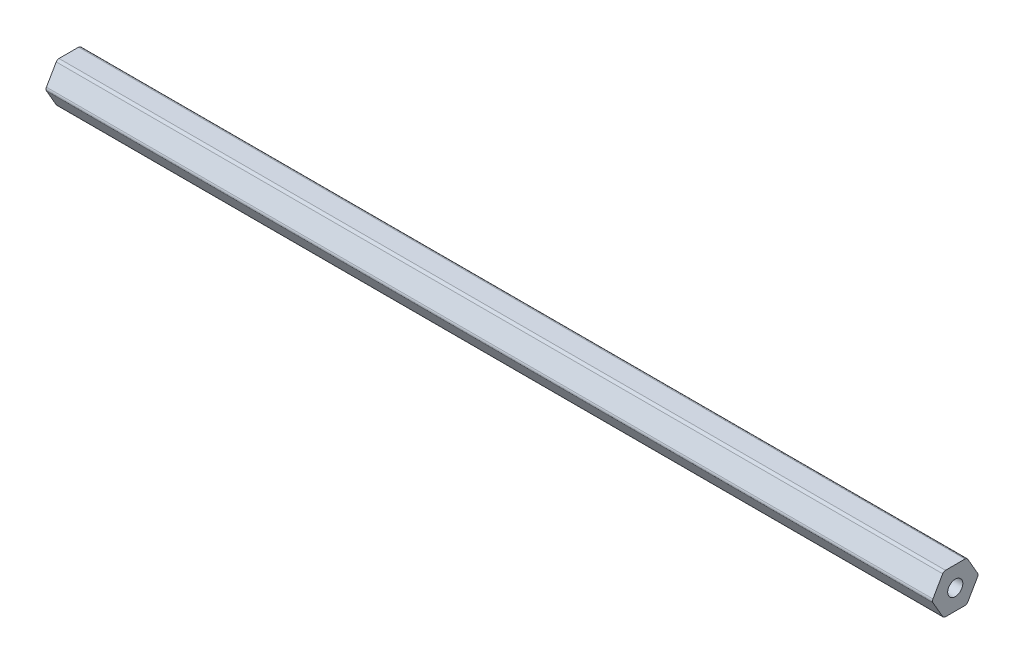
SolidWorks part; units mm, degrees
material "7075-T6 (SN)"
ref_plane "Front Plane" through (0, 0, 0) normal (0, 0, 1) x (1, 0, 0)
ref_plane "Top Plane" through (0, 0, 0) normal (0, 1, 0) x (1, 0, 0)
ref_plane "Right Plane" through (0, 0, 0) normal (1, 0, 0) x (0, 0, -1)
sketch "Sketch1" plane through (0, 0, 0) normal (1, 0, 0) x (0, 0, -1)
  line L1 (7.0391, 0.508) -> (3.9595, 5.842)
  line L2 (3.0796, 6.35) -> (-3.0796, 6.35)
  line L3 (-3.9595, 5.842) -> (-7.0391, 0.508)
  line L4 (-7.0391, -0.508) -> (-3.9595, -5.842)
  line L5 (-3.0796, -6.35) -> (3.0796, -6.35)
  line L6 (3.9595, -5.842) -> (7.0391, -0.508)
  circle A0 centre (0, 0) radius 6.35 construction
  arc A1 (3.0796, 6.35) -> (3.9595, 5.842) centre (3.0796, 5.334) cw
  arc A2 (7.0391, 0.508) -> (7.0391, -0.508) centre (6.1592, 0) cw
  arc A3 (3.9595, -5.842) -> (3.0796, -6.35) centre (3.0796, -5.334) cw
  arc A4 (-3.0796, -6.35) -> (-3.9595, -5.842) centre (-3.0796, -5.334) cw
  arc A5 (-7.0391, -0.508) -> (-7.0391, 0.508) centre (-6.1592, 0) cw
  arc A6 (-3.9595, 5.842) -> (-3.0796, 6.35) centre (-3.0796, 5.334) cw
  circle A7 centre (0, 0) radius 2.3813
  point P11 (3.6662, 6.35)
  point P14 (7.3323, 0)
  dimension "D1" = 12.7
  dimension "D3" = 1.016
  dimension "D4" = 4.7625
  dimension "D2" = 6.35
extrude "Boss-Extrude1" add sketch "Sketch1" along normal blind 279.4
